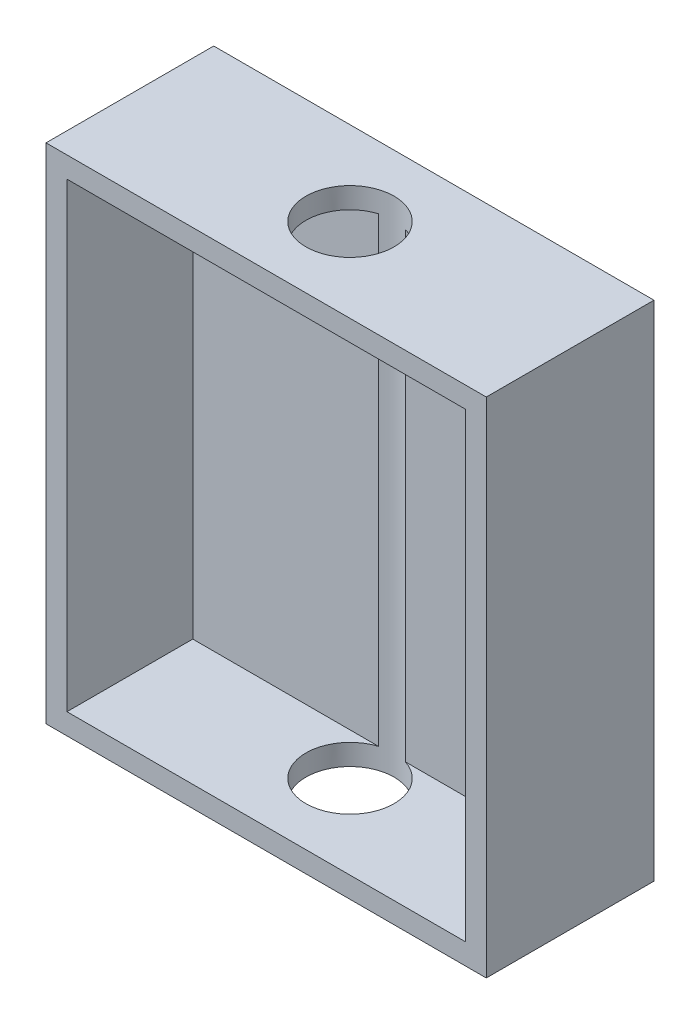
SolidWorks part; units mm, degrees
material "ABS PC"
ref_plane "Front Plane" through (0, 0, 0) normal (0, 0, 1) x (1, 0, 0)
ref_plane "Top Plane" through (0, 0, 0) normal (0, 1, 0) x (1, 0, 0)
ref_plane "Right Plane" through (0, 0, 0) normal (1, 0, 0) x (0, 0, -1)
sketch "Sketch1" plane through (0, 0, 0) normal (0, 0, 1) x (1, 0, 0)
  line L1 (-10.5, -12) -> (10.5, -12)
  line L2 (-10.5, -12) -> (-10.5, 12)
  line L3 (-10.5, 12) -> (10.5, 12)
  line L4 (10.5, -12) -> (10.5, 12)
  line L5 (-10.5, -12) -> (10.5, 12) construction
  line L6 (-10.5, 12) -> (10.5, -12) construction
  line L7 (-9.5, -11) -> (9.5, -11)
  line L8 (-9.5, -11) -> (-9.5, 11)
  line L9 (-9.5, 11) -> (9.5, 11)
  line L10 (9.5, -11) -> (9.5, 11)
  line L11 (-9.5, -11) -> (9.5, 11) construction
  line L12 (-9.5, 11) -> (9.5, -11) construction
  point P0 (0, 0)
  point P5 (0, 0)
  dimension "D1" = 24
  dimension "D2" = 21
  dimension "D3" = 19
  dimension "D4" = 22
extrude "Boss-Extrude1" add sketch "Sketch1" along normal blind 8
sketch "Sketch2" plane through (0, 0, 0) normal (0, 0, -1) x (-1, 0, 0)
  line L1 (-9.5, -11) -> (9.5, -11)
  line L2 (-9.5, -11) -> (-9.5, 11)
  line L3 (-9.5, 11) -> (9.5, 11)
  line L4 (9.5, -11) -> (9.5, 11)
  line L5 (-9.5, -11) -> (9.5, 11) construction
  line L6 (-9.5, 11) -> (9.5, -11) construction
  point P0 (0, 0)
extrude "Boss-Extrude2" add sketch "Sketch2" against normal blind 2
sketch "Sketch3" plane through (0, -12, 0) normal (0, -1, 0) x (1, 0, 0)
  line L0 (0, 8) -> (0, 4)
  line L1 (-10.5, 8) -> (10.5, 8) construction
  circle A0 centre (0, 4) radius 2.1
  dimension "D2" = 4.2
  dimension "D1" = 4
extrude "Cut-Extrude1" cut sketch "Sketch3" against normal blind 30
